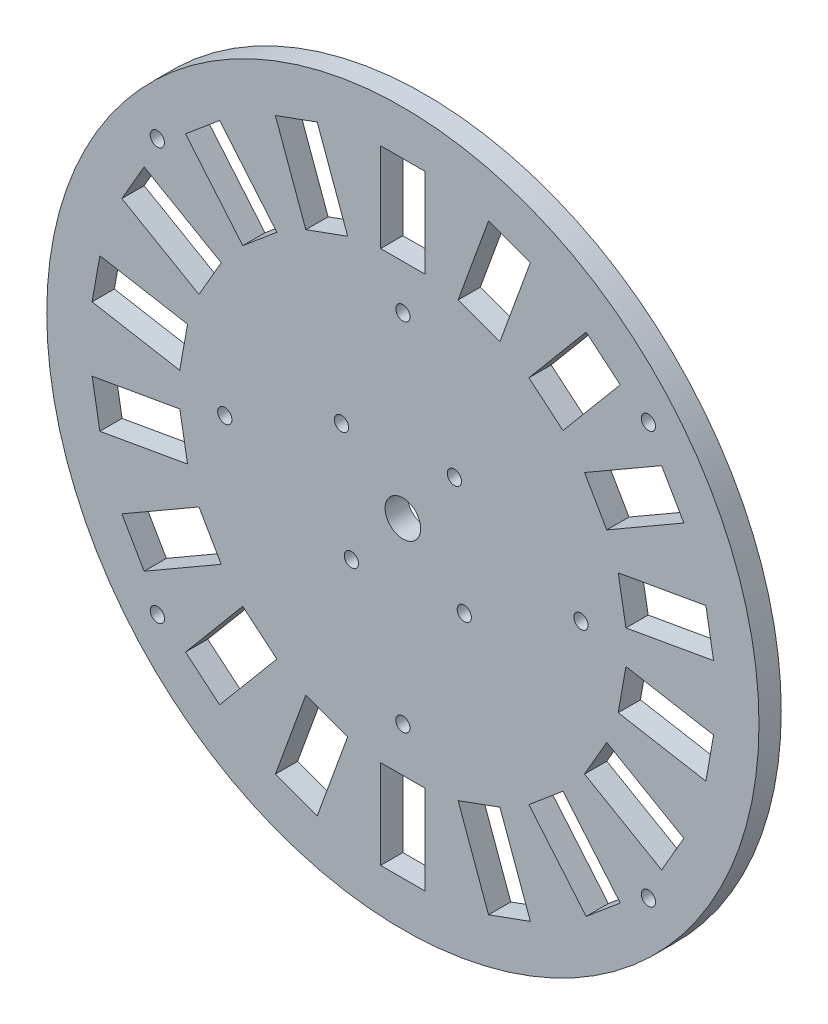
SolidWorks part; units mm, degrees
ref_plane "Front Plane" through (0, 0, 0) normal (0, 0, 1) x (1, 0, 0)
ref_plane "Top Plane" through (0, 0, 0) normal (0, 1, 0) x (1, 0, 0)
ref_plane "Right Plane" through (0, 0, 0) normal (1, 0, 0) x (0, 0, -1)
sketch "Sketch1" plane through (0, 0, 0) normal (0, 0, 1) x (1, 0, 0)
  circle A0 centre (0, 0) radius 80
  dimension "D1" = 160
extrude "Boss-Extrude1" add sketch "Sketch1" along normal blind 5
sketch "Sketch2" plane through (0, 0, 5) normal (0, 0, 1) x (1, 0, 0)
  line L0 (0, 0) -> (0, 45) construction
  line L1 (-5, 50) -> (5, 50)
  line L3 (-5, 50) -> (-5, 70)
  line L5 (5, 50) -> (5, 70)
  line L6 (-5, 70) -> (5, 70)
  arc A0 (-5, 50) -> (5, 50) centre (0, 50) ccw construction
  arc A1 (5, 70) -> (-5, 70) centre (0, 67.7087) ccw construction
  circle A2 centre (0, 0) radius 4
  dimension "D2" = 10
  dimension "D1" = 50
  dimension "D3" = 20
extrude "Cut-Extrude1" cut sketch "Sketch2" against normal blind 5
pattern_circular "CirPattern1" count 18 over 360 about axis through (0, 0, 0) along (0, 0, 1) of "Cut-Extrude1"
sketch "Sketch3" plane through (0, 0, 5) normal (0, 0, 1) x (1, 0, 0)
  line L0 (0, 0) -> (-55.1552, 46.2807) construction
  line L1 (0, 0) -> (-55.1552, -46.2807) construction
  line L2 (0, 9.5844) -> (0, -14.2114) construction
  line L3 (0, 0) -> (55.1552, -46.2807) construction
  line L4 (0, 0) -> (55.1552, 46.2807) construction
  line L5 (40, 0) -> (-40, 0) construction
  line L6 (0, -40) -> (0, 40) construction
  circle A0 centre (-55.1552, 46.2807) radius 1.6
  circle A1 centre (-55.1552, -46.2807) radius 1.6
  circle A2 centre (55.1552, -46.2807) radius 1.6
  circle A3 centre (55.1552, 46.2807) radius 1.6
  circle A4 centre (-40, 0) radius 1.6
  circle A5 centre (0, 40) radius 1.6
  circle A6 centre (0, -40) radius 1.6
  circle A7 centre (40, 0) radius 1.6
  dimension "D2" = 3.2
  dimension "D3" = 3.2
  dimension "D6" = 72
  dimension "D7" = 3.2
  dimension "D1" = 72
  dimension "D4" = 80
  dimension "D5" = 100
  dimension "D8" = 40
extrude "Cut-Extrude2" cut sketch "Sketch3" against normal blind 5
sketch "Sketch4" plane through (0, 0, 0) normal (0, 0, -1) x (-1, 0, 0)
  line L0 (0, 0) -> (-11.5702, 13.7888) construction
  line L2 (0, 0) -> (0, 45) construction
  circle A0 centre (-11.5702, 13.7888) radius 1.6
  circle A4 centre (13.7888, 11.5702) radius 1.6
  circle A5 centre (11.5702, -13.7888) radius 1.6
  circle A6 centre (-13.7888, -11.5702) radius 1.6
  dimension "D2" = 3.2
  dimension "D1" = 18
  dimension "D4" = 40
  dimension "D3" = 4
extrude "Cut-Extrude3" cut sketch "Sketch4" against normal blind 10
